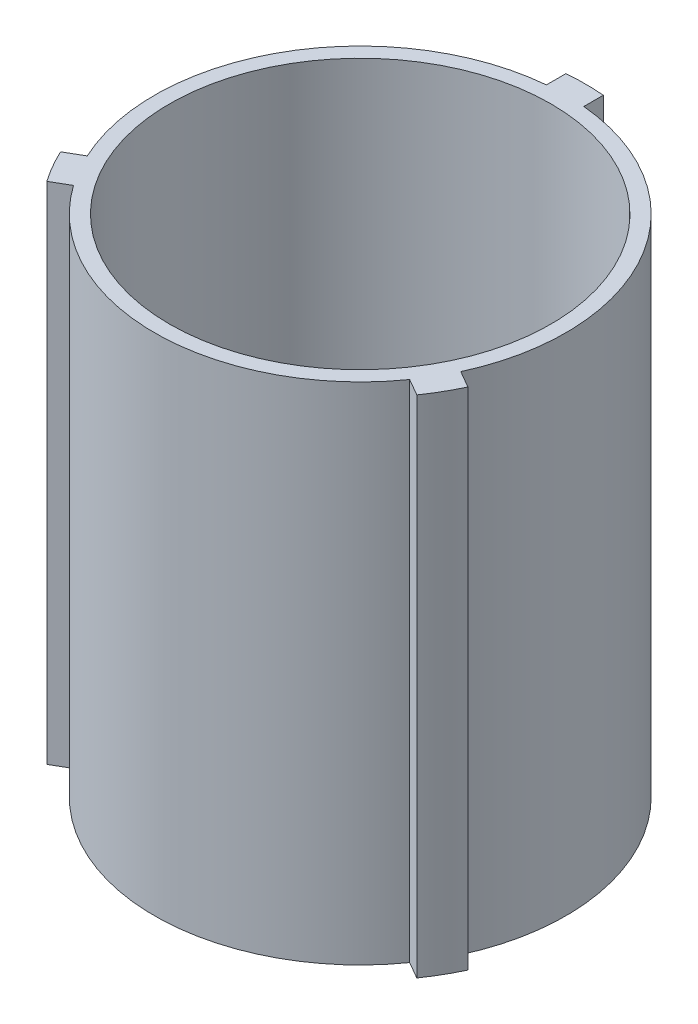
SolidWorks part; units mm, degrees
ref_plane "Front Plane" through (0, 0, 0) normal (0, 0, 1) x (1, 0, 0)
ref_plane "Top Plane" through (0, 0, 0) normal (0, 1, 0) x (1, 0, 0)
ref_plane "Right Plane" through (0, 0, 0) normal (1, 0, 0) x (0, 0, -1)
sketch "Sketch1" plane through (0, 0, 0) normal (0, 1, 0) x (1, 0, 0)
  line L0 (-3.175, 34.7804) -> (-3.175, 38.0949)
  line L1 (3.175, 34.7804) -> (-3.175, 34.7804) construction
  line L2 (3.175, 38.0949) -> (3.175, 34.7804)
  line L3 (31.7082, -14.6406) -> (34.5787, -16.2978)
  line L5 (31.4037, -21.7971) -> (28.5332, -20.1398)
  line L6 (-28.5332, -20.1398) -> (-31.4037, -21.7971)
  line L8 (-34.5787, -16.2978) -> (-31.7082, -14.6406)
  arc A0 (-34.5787, -16.2978) -> (-31.4037, -21.7971) centre (0, 0) ccw
  arc A1 (-28.5332, -20.1398) -> (28.5332, -20.1398) centre (0, 0) ccw
  arc A2 (3.175, 38.0949) -> (-3.175, 38.0949) centre (0, 0) ccw
  arc A3 (31.4037, -21.7971) -> (34.5787, -16.2978) centre (0, 0) ccw
  arc A4 (-3.175, 34.7804) -> (-31.7082, -14.6406) centre (0, 0) ccw
  arc A5 (31.7082, -14.6406) -> (3.175, 34.7804) centre (0, 0) ccw
  circle A6 centre (0, 0) radius 32.385
  point P3 (0, 34.7804)
  point P19 (0, 0)
  dimension "D1" = 76.454
  dimension "D4" = 69.85
  dimension "D5" = 64.77
  dimension "D2" = 6.35
  dimension "D3" = 3
extrude "Boss-Extrude1" add sketch "Sketch1" along normal blind 85.725
